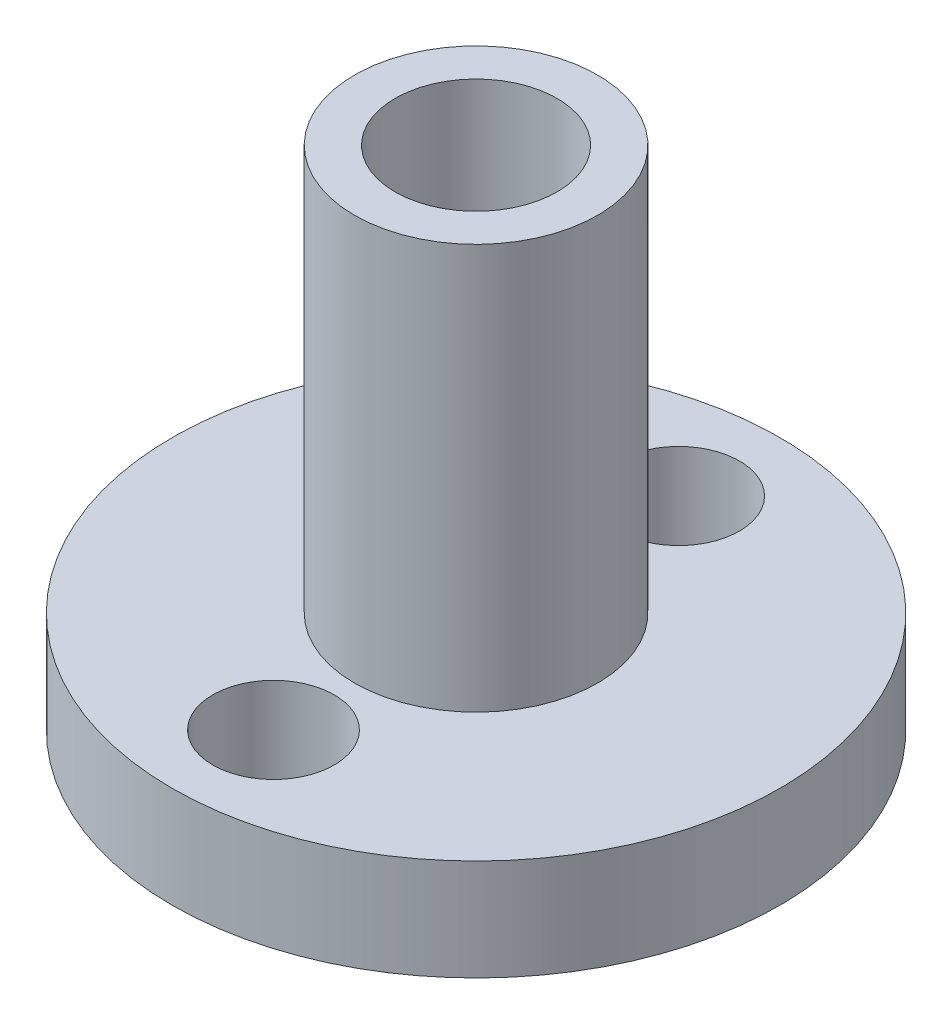
SolidWorks part; units mm, degrees
material "AISI 1020"
ref_plane "Front Plane" through (0, 0, 0) normal (0, 0, 1) x (1, 0, 0)
ref_plane "Top Plane" through (0, 0, 0) normal (0, 1, 0) x (1, 0, 0)
ref_plane "Right Plane" through (0, 0, 0) normal (1, 0, 0) x (0, 0, -1)
sketch "Sketch1" plane through (0, 0, 0) normal (0, 1, 0) x (1, 0, 0)
  circle A0 centre (0, 0) radius 15
  circle A2 centre (0, 10) radius 3
  circle A3 centre (0, -10) radius 3
  dimension "D1" = 30
  dimension "D3" = 3
  dimension "D4" = 3
  dimension "D5" = 10
  dimension "D6" = 10
extrude "Boss-Extrude1" add sketch "Sketch1" along normal blind 5
sketch "Sketch2" plane through (0, 5, 0) normal (0, 1, 0) x (1, 0, 0)
  circle A0 centre (0, 0) radius 6
  circle A1 centre (0, 0) radius 4
  dimension "D1" = 12
  dimension "D2" = 8
extrude "Boss-Extrude2" add sketch "Sketch2" along normal blind 20
sketch "Sketch3" plane through (0, 0, 0) normal (0, -1, 0) x (1, 0, 0)
  line L1 (0, 15) -> (0, -15) construction
  circle A1 centre (0, 0) radius 15 construction
  point P5 (0, 0)
